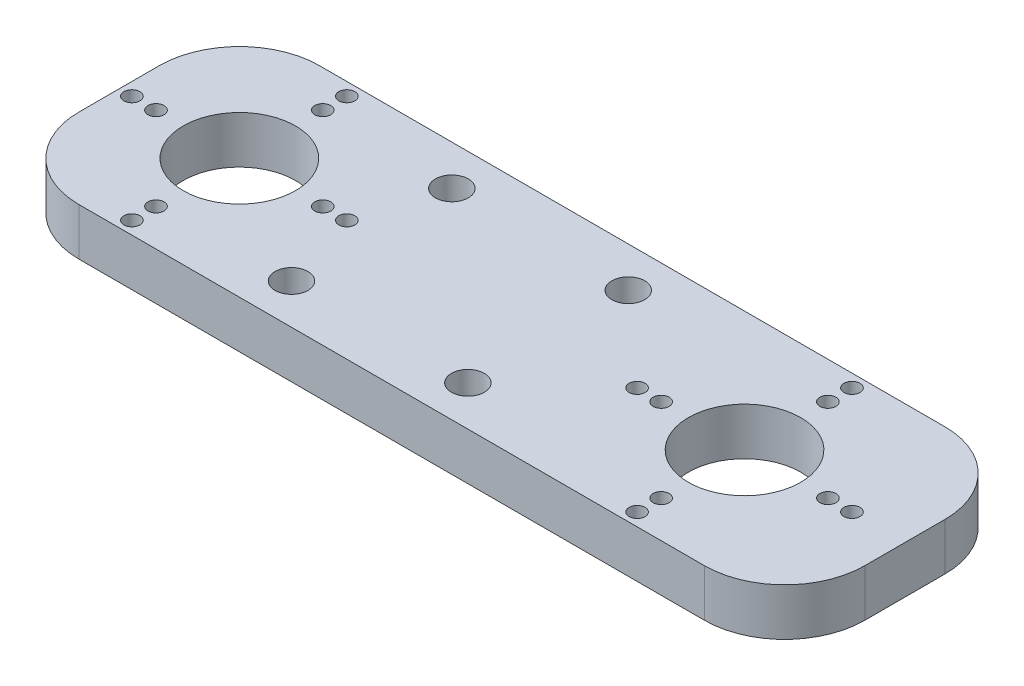
SolidWorks part; units mm, degrees
ref_plane "Front Plane" through (0, 0, 0) normal (0, 0, 1) x (1, 0, 0)
ref_plane "Top Plane" through (0, 0, 0) normal (0, 1, 0) x (1, 0, 0)
ref_plane "Right Plane" through (0, 0, 0) normal (1, 0, 0) x (0, 0, -1)
sketch "Sketch1" plane through (0, 0, 0) normal (0, 1, 0) x (1, 0, 0)
  line L1 (-49, -15) -> (49, -15)
  line L2 (-49, -15) -> (-49, 15)
  line L3 (-49, 15) -> (49, 15)
  line L4 (49, -15) -> (49, 15)
  line L5 (-49, -15) -> (49, 15) construction
  line L6 (-49, 15) -> (49, -15) construction
  circle A0 centre (-34, 0) radius 7
  circle A2 centre (-44.4, 0) radius 1
  circle A9 centre (-47.4, 0) radius 1
  circle A10 centre (-34, 10.4) radius 1
  circle A11 centre (-34, 13.4) radius 1
  circle A12 centre (-23.6, 0) radius 1
  circle A13 centre (-20.6, 0) radius 1
  circle A14 centre (-34, -10.4) radius 1
  circle A15 centre (-34, -13.4) radius 1
  point P0 (0, 0)
  point P26 (-34, 0)
  point P27 (-34, 0)
  dimension "D6" = 14
  dimension "D7" = 15
  dimension "D3" = 10.4
  dimension "D4" = 2
  dimension "D10" = 3
  dimension "D1" = 30
  dimension "D2" = 98
  dimension "D5" = 4
extrude "Boss-Extrude1" add sketch "Sketch1" along normal blind 5.9
sketch "Sketch4" plane through (0, 5.9, 0) normal (0, 1, 0) x (1, 0, 0)
  line L0 (49, -15) -> (49, 15) construction
  line L1 (-1.5, -10) -> (39, -10) construction
  line L2 (-1.5, -10) -> (-1.5, 10) construction
  line L3 (-1.5, 10) -> (39, 10) construction
  line L4 (39, -10) -> (39, 10) construction
  line L5 (-1.5, -10) -> (39, 10) construction
  line L6 (-1.5, 10) -> (39, -10) construction
  line L7 (-2.5, 15) -> (-2.5, -15) construction
  line L8 (49, 15) -> (-49, 15) construction
  line L9 (-49, -15) -> (49, -15) construction
  circle A9 centre (-34, 0) radius 7 construction
  circle A10 centre (-34, 0) radius 7
  circle A15 centre (-34, -13.4) radius 1 construction
  circle A16 centre (-34, -10.4) radius 1 construction
  circle A17 centre (-44.4, 0) radius 1 construction
  circle A18 centre (-47.4, 0) radius 1 construction
  circle A19 centre (-34, 13.4) radius 1 construction
  circle A20 centre (-23.6, 0) radius 1 construction
  circle A21 centre (-20.6, 0) radius 1 construction
  circle A22 centre (-34, 10.4) radius 1 construction
  circle A23 centre (-34, -13.4) radius 1
  circle A24 centre (-34, -10.4) radius 1
  circle A25 centre (-44.4, 0) radius 1
  circle A26 centre (-47.4, 0) radius 1
  circle A27 centre (-34, 13.4) radius 1
  circle A28 centre (-23.6, 0) radius 1
  circle A29 centre (-20.6, 0) radius 1
  circle A30 centre (-34, 10.4) radius 1
  circle A31 centre (29, -13.4) radius 1
  circle A32 centre (29, -10.4) radius 1
  circle A33 centre (42.4, 0) radius 1
  circle A34 centre (39.4, 0) radius 1
  circle A35 centre (29, 0) radius 7
  circle A36 centre (29, 10.4) radius 1
  circle A37 centre (29, 13.4) radius 1
  circle A38 centre (18.6, 0) radius 1
  circle A39 centre (15.6, 0) radius 1
  point P0 (18.75, 0)
  point P29 (29, 0)
  dimension "D4" = 10
  dimension "D1" = 40.5
  dimension "D2" = 20
  dimension "D3" = 10
extrude "Cut-Extrude3" cut sketch "Sketch4" against normal blind 10
fillet "Fillet1" radius 10 4 edges at (49, 2.95, 15) (49, 2.95, -15) (-49, 2.95, 15) (-49, 2.95, -15)
sketch "Sketch5" plane through (0, 5.9, 0) normal (0, 1, 0) x (1, 0, 0)
  line L0 (-17.5, 10) -> (-17.5, 0) construction
  line L3 (-17.5, 0) -> (0, 0) construction
  line L6 (-17.5, 0) -> (-17.5, -10) construction
  line L8 (-49, 5) -> (-49, -5) construction
  line L9 (-6.5, 0) -> (-6.5, 15) construction
  line L10 (39, 15) -> (-39, 15) construction
  circle A0 centre (-17.5, 10) radius 2.05
  circle A1 centre (-17.5, -10) radius 2.05
  circle A2 centre (4.5, -10) radius 2.05
  circle A3 centre (4.5, 10) radius 2.05
  dimension "D2" = 4.1
  dimension "D1" = 31.5
  dimension "D3" = 11
  dimension "D4" = 20
extrude "Cut-Extrude4" cut sketch "Sketch5" against normal blind 10
equation "\"e\" = 5.9"
equation "\"D1@Boss-Extrude1\"= \"e\""
